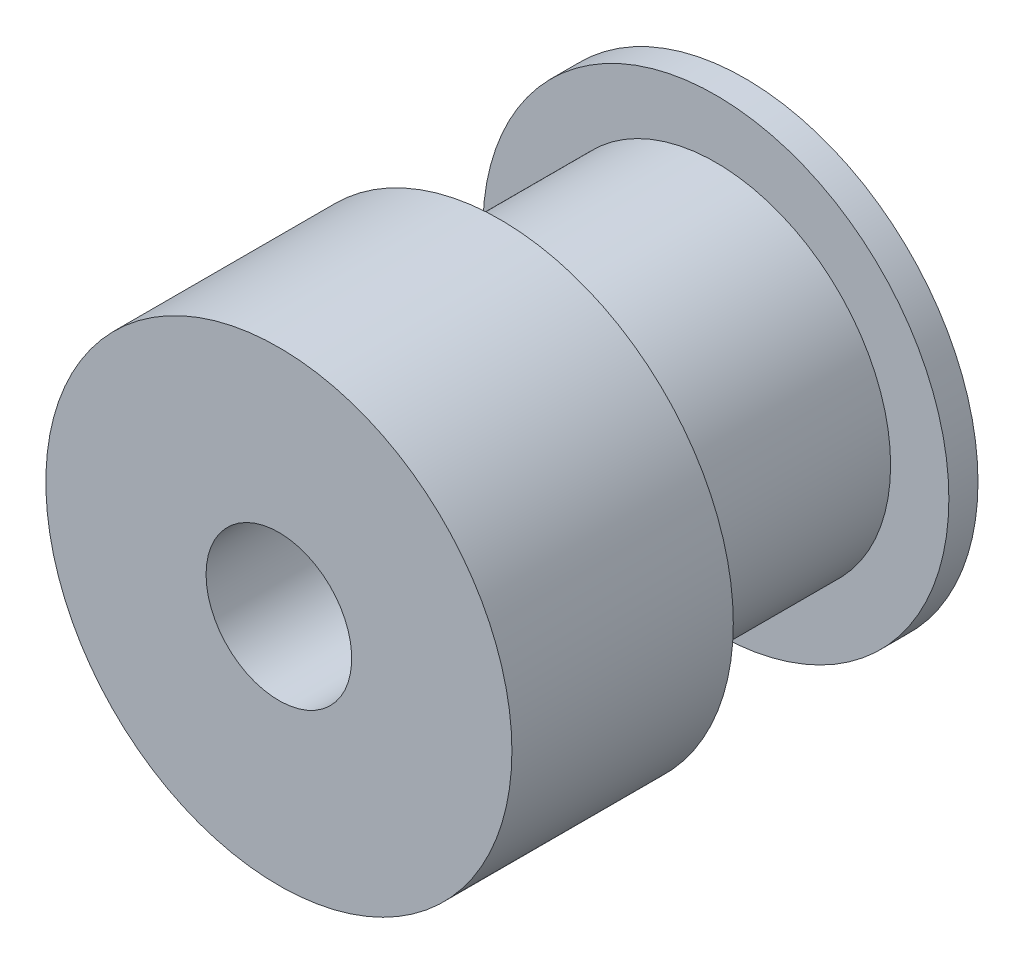
SolidWorks part; units mm, degrees
ref_plane "前视基准面" through (0, 0, 0) normal (0, 0, 1) x (1, 0, 0)
ref_plane "上视基准面" through (0, 0, 0) normal (0, 1, 0) x (1, 0, 0)
ref_plane "右视基准面" through (0, 0, 0) normal (1, 0, 0) x (0, 0, -1)
sketch "草图1" plane through (0, 0, 0) normal (0, 0, 1) x (1, 0, 0)
  circle A0 centre (0, 0) radius 8
  dimension "D1" = 16
extrude "凸台-拉伸1" add sketch "草图1" along normal blind 1
sketch "草图2" plane through (0, 0, 1) normal (0, 0, 1) x (1, 0, 0)
  circle A0 centre (0, 0) radius 6
  dimension "D1" = 12
extrude "凸台-拉伸2" add sketch "草图2" along normal blind 7.4
sketch "草图3" plane through (0, 0, 8.4) normal (0, 0, 1) x (1, 0, 0)
  circle A0 centre (0, 0) radius 8
  dimension "D1" = 16
extrude "凸台-拉伸3" add sketch "草图3" along normal blind 7.6
sketch "草图4" plane through (0, 0, 0) normal (0, 0, -1) x (-1, 0, 0)
  circle A0 centre (0, 0) radius 2.5
  dimension "D1" = 5
extrude "切除-拉伸1" cut sketch "草图4" against normal through all
